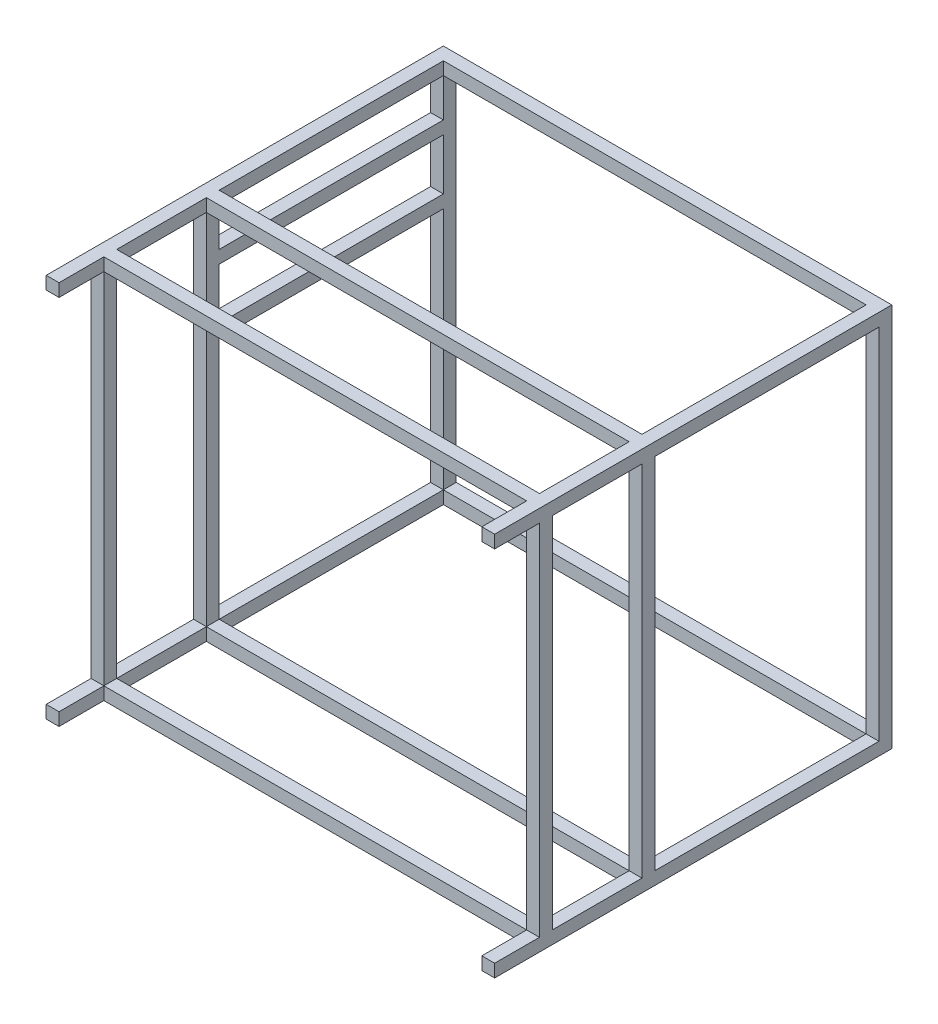
SolidWorks part; units mm, degrees
ref_plane "Front Plane" through (0, 0, 0) normal (0, 0, 1) x (1, 0, 0)
ref_plane "Top Plane" through (0, 0, 0) normal (0, 1, 0) x (1, 0, 0)
ref_plane "Right Plane" through (0, 0, 0) normal (1, 0, 0) x (0, 0, -1)
sketch "Sketch8" plane through (0, 0, 4.8721) normal (0, 0, -1) x (-1, 0, 0)
  line L0 (-150, 100) -> (-1050, 100) construction
  line L1 (-1050, 700) -> (-1030, 700)
  line L2 (-1050, 700) -> (-1050, 680)
  line L3 (-1050, 680) -> (-1030, 680)
  line L4 (-1030, 700) -> (-1030, 680)
  line L13 (-1050, 100) -> (-1030, 100)
  line L14 (-1050, 100) -> (-1050, 120)
  line L15 (-1050, 120) -> (-1030, 120)
  line L16 (-1030, 100) -> (-1030, 120)
  line L17 (-1050, 100) -> (-1050, 700) construction
  dimension "D1" = 20
  dimension "D2" = 20
extrude "Boss-Extrude5" add sketch "Sketch8" along normal blind 600
sketch "Sketch10" plane through (0, 0, -595.1279) normal (0, 0, -1) x (-1, 0, 0)
  line L9 (-1050, 100) -> (-150, 100)
  line L10 (-1050, 100) -> (-1050, 700)
  line L11 (-1050, 700) -> (-150, 700)
  line L12 (-150, 100) -> (-150, 700)
  line L13 (-1030, 120) -> (-170, 120)
  line L14 (-1030, 120) -> (-1030, 680)
  line L15 (-1030, 680) -> (-170, 680)
  line L16 (-170, 120) -> (-170, 680)
  dimension "D1" = 900
  dimension "D2" = 20
extrude "Boss-Extrude6" add sketch "Sketch10" along normal blind 20
ref_plane "Plane12" through (0, 0, -245.1279) normal (0, 0, 1) x (1, 0, 0)
sketch "Sketch12" plane through (0, 0, -245.1279) normal (0, 0, 1) x (1, 0, 0)
  line L1 (170, 680) -> (1030, 680)
  line L2 (170, 680) -> (170, 120)
  line L3 (170, 120) -> (1030, 120)
  line L4 (1030, 680) -> (1030, 120)
  line L5 (150, 700) -> (1050, 700)
  line L6 (150, 700) -> (150, 100)
  line L7 (150, 100) -> (1050, 100)
  line L8 (1050, 700) -> (1050, 100)
extrude "Boss-Extrude7" add sketch "Sketch12" along normal blind 20
sketch "Sketch13" plane through (0, 0, -615.1279) normal (0, 0, -1) x (-1, 0, 0)
  line L0 (-170, 680) -> (-1030, 680) construction
  line L1 (-370, 680) -> (-350, 680)
  line L2 (-370, 680) -> (-370, 120)
  line L3 (-370, 120) -> (-350, 120)
  line L4 (-350, 680) -> (-350, 120)
  line L5 (-1030, 120) -> (-170, 120) construction
  line L6 (-1050, 700) -> (-1050, 100) construction
  dimension "D1" = 20
  dimension "D2" = 680
extrude "Boss-Extrude8" add sketch "Sketch13" against normal blind 20
ref_plane "Plane13" through (0, 0, -420.1279) normal (0, 0, -1) x (-1, 0, 0)
mirror "Mirror1" about plane through (0, 0, -420.1279) normal (0, 0, -1) of "Boss-Extrude8"
sketch "Sketch14" plane through (0, 0, -245.1279) normal (0, 0, -1) x (-1, 0, 0)
  line L0 (-370, 680) -> (-370, 120) construction
  line L1 (-370, 600) -> (-350, 600)
  line L2 (-370, 600) -> (-370, 620)
  line L3 (-370, 620) -> (-350, 620)
  line L4 (-350, 600) -> (-350, 620)
  line L5 (-350, 120) -> (-350, 680) construction
  line L6 (-1030, 700) -> (-150, 700) construction
  dimension "D1" = 20
  dimension "D2" = 80
extrude "Boss-Extrude9" add sketch "Sketch14" along normal up to next (350 mm away)
ref_plane "Plane14" through (0, 560, 0) normal (0, -1, 0) x (-1, 0, 0)
mirror "Mirror2" about plane through (0, 560, 0) normal (0, -1, 0) of "Boss-Extrude9"
ref_plane "Plane15" through (0, 0, -85.1279) normal (0, 0, 1) x (1, 0, 0)
sketch "Sketch16" plane through (0, 0, -85.1279) normal (0, 0, 1) x (1, 0, 0)
  line L1 (170, 680) -> (1030, 680)
  line L2 (170, 680) -> (170, 120)
  line L3 (170, 120) -> (1030, 120)
  line L4 (1030, 680) -> (1030, 120)
  line L5 (150, 700) -> (1050, 700)
  line L6 (150, 700) -> (150, 100)
  line L7 (150, 100) -> (1050, 100)
  line L8 (1050, 700) -> (1050, 100)
extrude "Boss-Extrude10" add sketch "Sketch16" along normal blind 20
sketch "Sketch17" plane through (0, 700, 0) normal (0, 1, 0) x (1, 0, 0)
  line L0 (150, -4.8721) -> (170, -4.8721) construction
  line L1 (150, 615.1279) -> (350, 615.1279)
  line L2 (150, 615.1279) -> (150, -4.8721)
  line L3 (150, -4.8721) -> (350, -4.8721)
  line L4 (350, 615.1279) -> (350, -4.8721)
  line L5 (350, 595.1279) -> (350, 245.1279) construction
extrude "Cut-Extrude1" cut sketch "Sketch17" against normal through all
sketch "Sketch18" plane through (0, 0, -615.1279) normal (0, 0, -1) x (-1, 0, 0)
  line L0 (-350, 700) -> (-1050, 700) construction
  line L9 (-350, 680) -> (-370, 680)
  line L10 (-350, 680) -> (-350, 700)
  line L11 (-350, 700) -> (-370, 700)
  line L12 (-370, 680) -> (-370, 700)
  line L13 (-1050, 100) -> (-350, 100) construction
  line L14 (-350, 120) -> (-370, 120)
  line L15 (-350, 120) -> (-350, 100)
  line L16 (-350, 100) -> (-370, 100)
  line L17 (-370, 120) -> (-370, 100)
  line L18 (-350, 100) -> (-350, 700) construction
extrude "Boss-Extrude11" add sketch "Sketch18" against normal blind 620
sketch "Sketch19" plane through (0, 680, 0) normal (0, -1, 0) x (1, 0, 0)
  line L5 (370, -85.1279) -> (370, -225.1279) construction
  line L6 (370, -85.1279) -> (350, -85.1279)
  line L7 (370, -85.1279) -> (370, -65.1279)
  line L8 (370, -65.1279) -> (350, -65.1279)
  line L9 (350, -85.1279) -> (350, -65.1279)
  line L10 (1030, -85.1279) -> (370, -85.1279) construction
  line L11 (1030, -65.1279) -> (370, -65.1279) construction
  point P4 (0, 0)
extrude "Boss-Extrude12" add sketch "Sketch19" along normal blind 560
